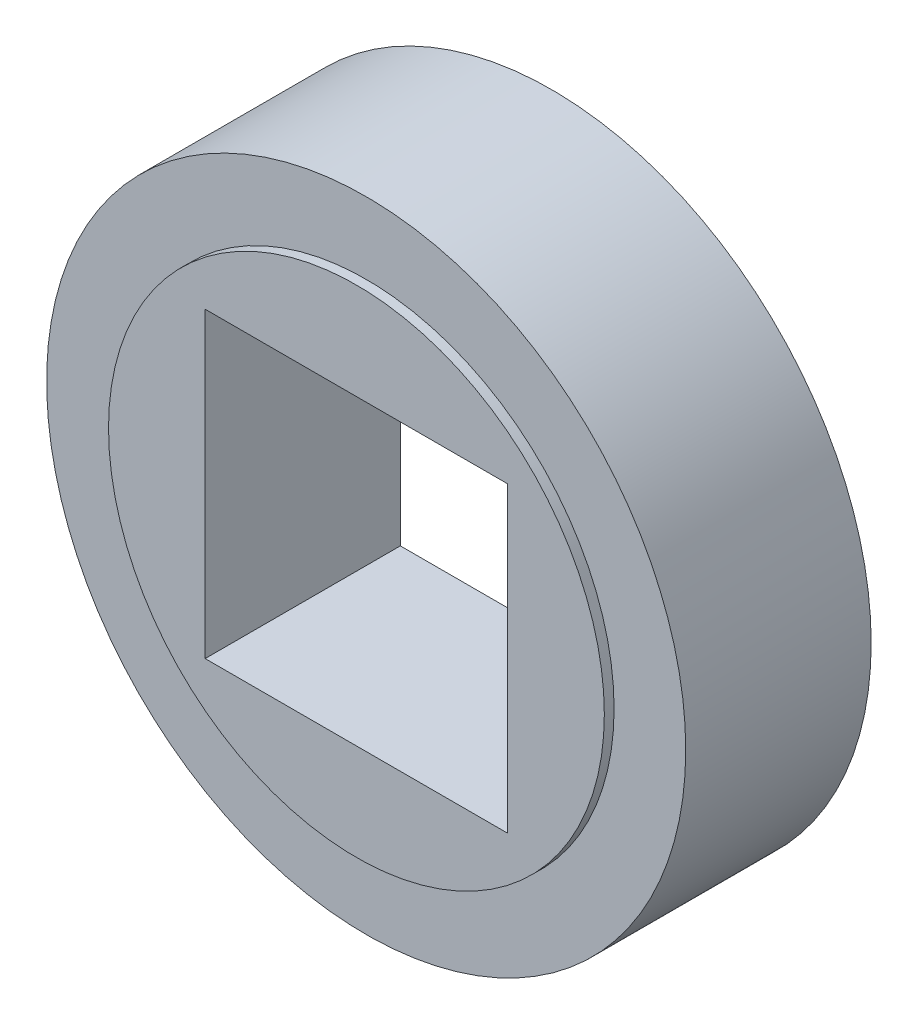
SolidWorks part; units mm, degrees
material "Choose your Material"
ref_plane "Front Plane" through (0, 0, 0) normal (0, 0, 1) x (1, 0, 0)
ref_plane "Top Plane" through (0, 0, 0) normal (0, 1, 0) x (1, 0, 0)
ref_plane "Right Plane" through (0, 0, 0) normal (1, 0, 0) x (0, 0, -1)
sketch "Sketch1" plane through (0, 0, 0) normal (0, 0, 1) x (1, 0, 0)
  line L1 (15.5, -15.5) -> (-15.5, -15.5)
  line L2 (15.5, -15.5) -> (15.5, 15.5)
  line L3 (15.5, 15.5) -> (-15.5, 15.5)
  line L4 (-15.5, -15.5) -> (-15.5, 15.5)
  line L5 (15.5, -15.5) -> (-15.5, 15.5) construction
  line L6 (15.5, 15.5) -> (-15.5, -15.5) construction
  circle A0 centre (0, 0) radius 32.7406
  point P0 (0, 0)
  dimension "D2" = 65.4812
  dimension "D1" = 31
extrude "Boss-Extrude1" add sketch "Sketch1" along normal blind 20
sketch "Sketch2" plane through (0, 0, 20) normal (0, 0, 1) x (1, 0, 0)
  circle A0 centre (0, 0) radius 25.4
  circle A1 centre (0, 0) radius 32.7406 construction
  circle A2 centre (0, 0) radius 32.7406
  dimension "D1" = 50.8
extrude "Cut-Extrude1" cut sketch "Sketch2" against normal blind 1
